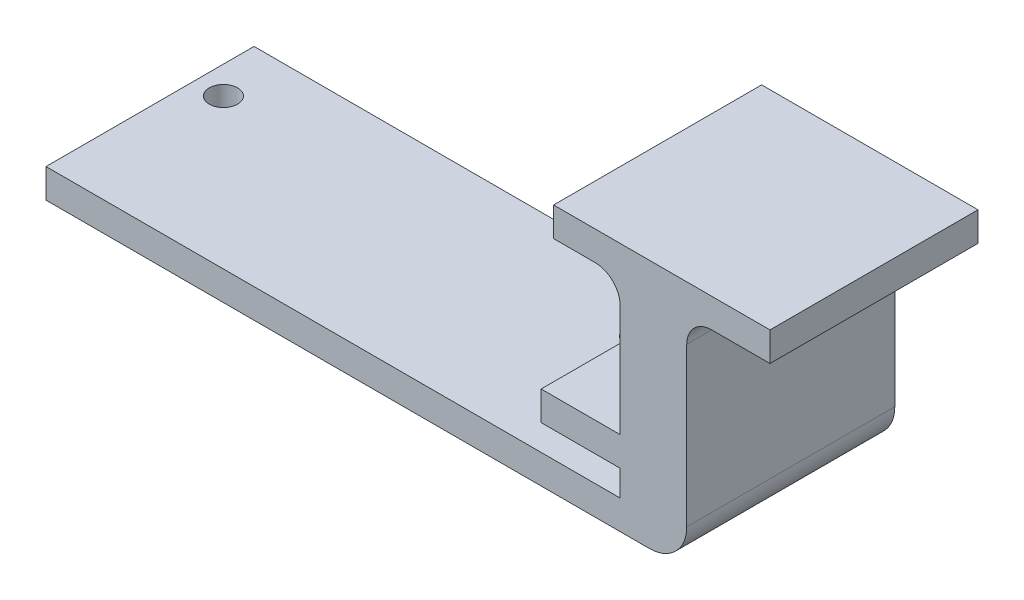
SolidWorks part; units mm, degrees
ref_plane "Piano frontale" through (0, 0, 0) normal (0, 0, 1) x (1, 0, 0)
ref_plane "Piano superiore" through (0, 0, 0) normal (0, 1, 0) x (1, 0, 0)
ref_plane "Piano destro" through (0, 0, 0) normal (1, 0, 0) x (0, 0, -1)
sketch "Schizzo1" plane through (0, 0, 0) normal (0, 0, 1) x (1, 0, 0)
  line L1 (70, -4.7081) -> (-7, -4.7081)
  line L2 (70, -4.7081) -> (70, -8.2081)
  line L3 (70, -8.2081) -> (-7, -8.2081)
  line L4 (-7, -4.7081) -> (-7, -8.2081)
  dimension "D1" = 77
  dimension "D2" = 3.5
extrude "Estrusione-Estrusione1" add sketch "Schizzo1" along normal blind 25
sketch "Schizzo2" plane through (0, -4.7081, 0) normal (0, 1, 0) x (1, 0, 0)
  line L0 (70, -25) -> (-7, -25) construction
  line L1 (70, 0) -> (62, 0)
  line L2 (70, 0) -> (70, -25)
  line L3 (70, -25) -> (62, -25)
  line L4 (62, 0) -> (62, -25)
  dimension "D1" = 8
extrude "Estrusione-Estrusione2" add sketch "Schizzo2" along normal blind 23
sketch "Schizzo3" plane through (62, 0, 0) normal (-1, 0, 0) x (0, 0, 1)
  line L0 (0, 18.2919) -> (0, -4.7081) construction
  line L1 (0, -1.6081) -> (25, -1.6081)
  line L2 (0, -1.6081) -> (0, 1.8919)
  line L3 (0, 1.8919) -> (25, 1.8919)
  line L4 (25, -1.6081) -> (25, 1.8919)
  line L5 (25, 18.2919) -> (25, -4.7081) construction
  line L6 (74, -2.2081) -> (0, -2.2081) construction
  dimension "D1" = 3.5
  dimension "D2" = 0.6
extrude "Estrusione-Estrusione3" add sketch "Schizzo3" along normal blind 9.5
sketch "Schizzo4" plane through (70, 0, 0) normal (1, 0, 0) x (0, 0, -1)
  line L1 (-25, 18.2919) -> (0, 18.2919)
  line L2 (-25, 18.2919) -> (-25, 21.7919)
  line L3 (-25, 21.7919) -> (0, 21.7919)
  line L4 (0, 18.2919) -> (0, 21.7919)
  dimension "D1" = 3.5
extrude "Estrusione-Estrusione4" add sketch "Schizzo4" along normal blind 10 and the other way blind 16
sketch "Schizzo5" plane through (0, -4.7081, 0) normal (0, 1, 0) x (1, 0, 0)
  circle A0 centre (46.3198, -7) radius 1.7
  circle A1 centre (-3.6802, -7) radius 1.7
extrude "Taglio-Estrusione1" cut sketch "Schizzo5" against normal blind 8
fillet "Raccordo2" radius 4.5 1 edges at (70, -8.2081, 12.5)
fillet "Raccordo3" radius 3 1 edges at (70, 18.2919, 12.5)
fillet "Raccordo5" radius 3 1 edges at (62, 18.2919, 12.5)
